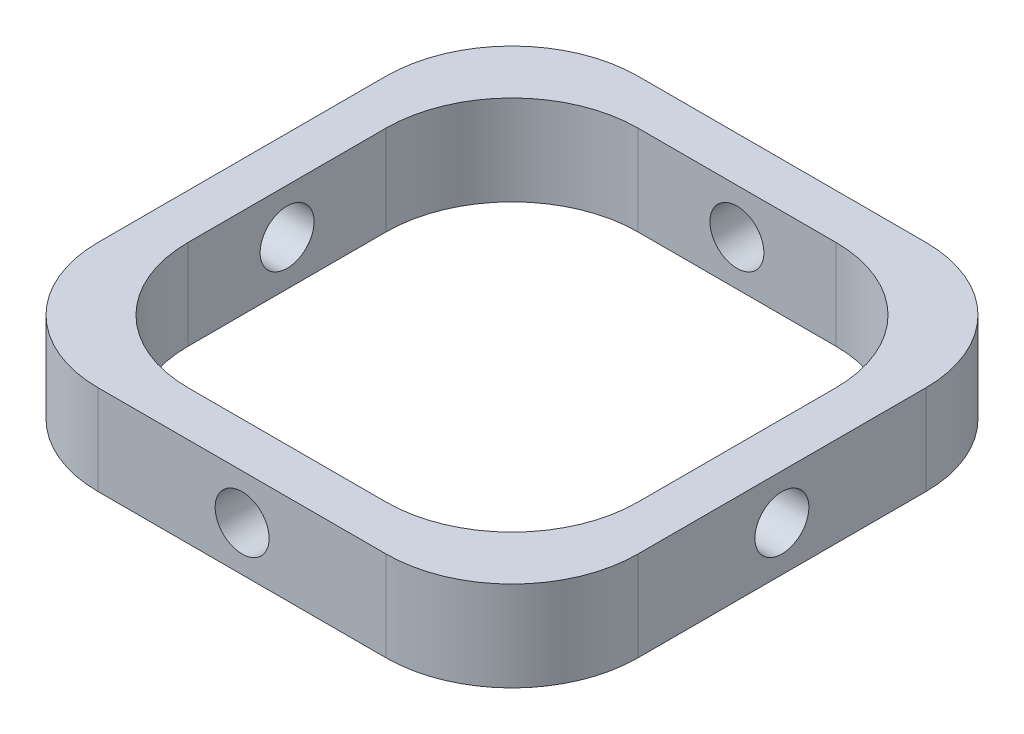
SolidWorks part; units mm, degrees
ref_plane "Alzado" through (0, 0, 0) normal (0, 0, 1) x (1, 0, 0)
ref_plane "Planta" through (0, 0, 0) normal (0, 1, 0) x (1, 0, 0)
ref_plane "Vista lateral" through (0, 0, 0) normal (1, 0, 0) x (0, 0, -1)
sketch "Croquis1" plane through (0, 0, 0) normal (0, 1, 0) x (1, 0, 0)
  line L0 (-12.5, 12.5) -> (12.5, 12.5)
  line L1 (-15, -15) -> (15, -15)
  line L2 (-15, -15) -> (-15, 15)
  line L3 (-15, 15) -> (15, 15)
  line L4 (15, -15) -> (15, 15)
  line L5 (-15, -15) -> (15, 15) construction
  line L6 (-15, 15) -> (15, -15) construction
  line L7 (12.5, -12.5) -> (12.5, 12.5)
  line L8 (-12.5, -12.5) -> (12.5, -12.5)
  line L9 (-12.5, -12.5) -> (-12.5, 12.5)
  point P0 (0, 0)
  dimension "D1" = 30
  dimension "D2" = 30
  dimension "D3" = 2.5
extrude "Saliente-Extruir1" add sketch "Croquis1" along normal blind 5
sketch "Croquis2" plane through (0, 0, 15) normal (0, 0, 1) x (1, 0, 0)
  line L0 (0, 0) -> (0, 5) construction
  line L1 (-15, 0) -> (15, 0) construction
  line L2 (-15, 5) -> (15, 5) construction
  circle A0 centre (0, 2.5) radius 1.5
  dimension "D1" = 3
extrude "Cortar-Extruir1" cut sketch "Croquis2" against normal through all both and the other way through all
sketch "Croquis3" plane through (-15, 0, 0) normal (-1, 0, 0) x (0, 0, 1)
  line L0 (0, 0) -> (0, 5) construction
  line L1 (-15, 5) -> (15, 5) construction
  circle A0 centre (0, 2.5) radius 1.5
  dimension "D1" = 3
extrude "Cortar-Extruir2" cut sketch "Croquis3" against normal through all both and the other way through all
sketch "Croquis4" plane through (0, 0, 0) normal (0, 1, 0) x (1, 0, 0)
  circle A0 centre (0, 0) radius 11
  dimension "D1" = 22
fillet "Redondeo1" radius 7 8 edges at (-15, 2.5, 15) (15, 2.5, 15) (15, 2.5, -15) (-15, 2.5, -15) (-12.5, 2.5, 12.5) (12.5, 2.5, 12.5) (12.5, 2.5, -12.5) (-12.5, 2.5, -12.5)
